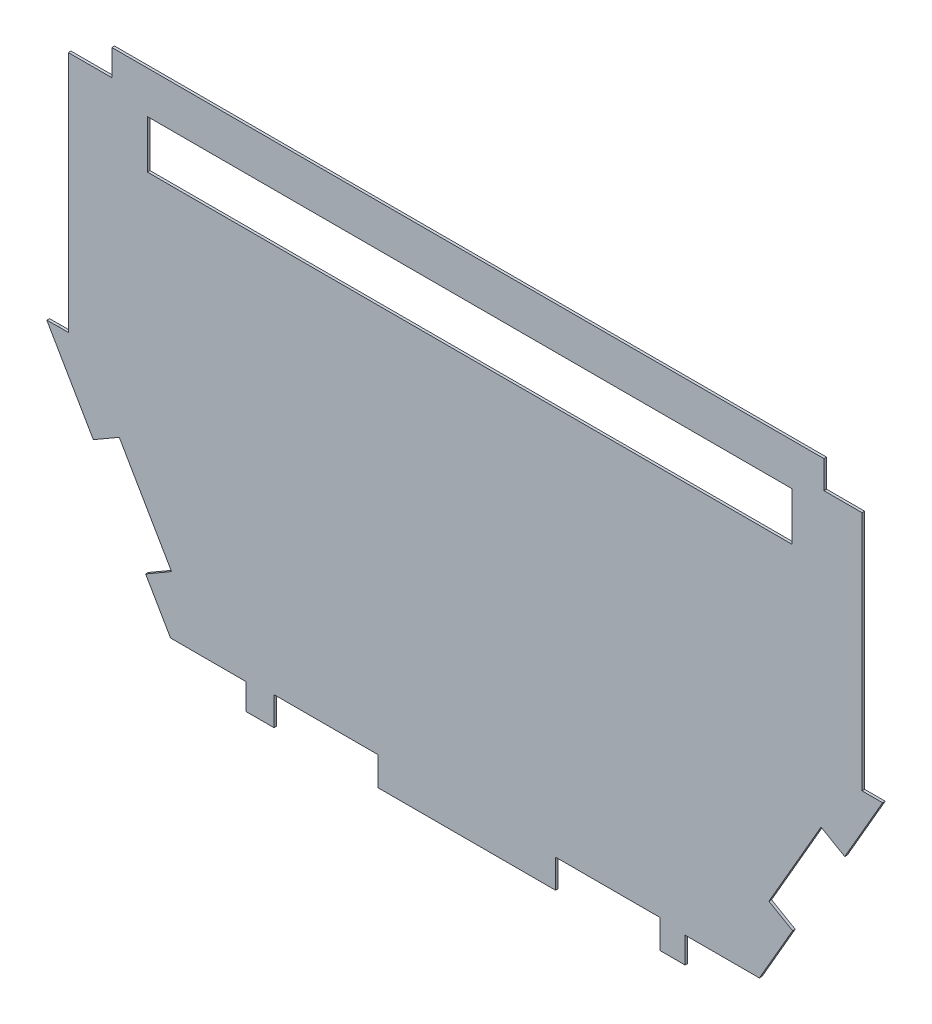
SolidWorks part; units mm, degrees
ref_plane "Front Plane" through (0, 0, 0) normal (0, 0, 1) x (1, 0, 0)
ref_plane "Top Plane" through (0, 0, 0) normal (0, 1, 0) x (1, 0, 0)
ref_plane "Right Plane" through (0, 0, 0) normal (1, 0, 0) x (0, 0, -1)
sketch "Sketch3" plane through (0, 0, 0) normal (0, 0, 1) x (1, 0, 0)
  line L3 (-216.9171, 295.8547) -> (-311.4999, 132.0324)
  line L4 (-368.5466, 112.1234) -> (-705.5135, 112.1234)
  line L7 (-813.3042, 502.1068) -> (-261.9807, 502.1052)
  line L11 (-841.9835, 482.0167) -> (-841.9835, 480.7707)
  line L14 (-232.6774, 480.7707) -> (-233.7869, 480.7707)
  line L16 (-212.2518, 452.135) -> (-212.1921, 346.8689)
  line L18 (-841.9835, 480.7707) -> (-841.9835, 452.932)
  line L21 (-841.9835, 482.0167) -> (-813.3042, 482.0167)
  line L22 (-813.3042, 482.0167) -> (-813.3042, 502.1068)
  line L23 (-862.9682, 452.932) -> (-841.9835, 452.932)
  line L24 (-261.9807, 480.7707) -> (-261.9807, 502.1052)
  line L25 (-233.7869, 480.7707) -> (-261.9807, 480.7707)
  line L26 (-232.6774, 480.7707) -> (-232.6774, 452.135)
  line L27 (-232.6774, 452.135) -> (-212.2518, 452.135)
  line L28 (-862.9682, 452.932) -> (-862.9682, 346.3054)
  line L29 (-212.1921, 346.8689) -> (-232.6774, 346.8689)
  line L30 (-232.6774, 346.8689) -> (-232.6774, 295.8547)
  line L31 (-232.6774, 295.8547) -> (-216.9171, 295.8547)
  line L32 (-368.5466, 112.1234) -> (-368.5466, 132.0324)
  line L33 (-368.5466, 132.0324) -> (-311.4999, 132.0324)
  line L34 (-705.5135, 112.1234) -> (-705.5135, 132.0324)
  line L35 (-705.5135, 132.0324) -> (-763.5115, 132.0324)
  line L36 (-862.9682, 346.3054) -> (-841.9835, 346.3054)
  line L37 (-842.7446, 346.3054) -> (-842.7446, 296.0768)
  line L38 (-842.7446, 296.0768) -> (-858.5136, 295.8547)
  line L39 (-858.5136, 295.8547) -> (-763.5115, 132.0324)
ref_plane "Plane1" through (0, 0, 0) normal (0, 0, 1) x (1, 0, 0)
sketch "Sketch4" plane through (0, 0, 0) normal (0, 0, 1) x (1, 0, 0)
  line L0 (-808.4973, 502.1068) -> (-261.9807, 502.1052)
  line L1 (-261.9807, 502.1052) -> (-261.9807, 480.7707)
  line L2 (-261.9807, 480.7707) -> (-232.6774, 480.7707)
  line L3 (-232.6774, 480.7707) -> (-232.6774, 452.135)
  line L4 (-232.6774, 452.135) -> (-212.2518, 452.135)
  line L5 (-212.2518, 452.135) -> (-212.1921, 346.8689)
  line L6 (-212.1921, 346.8689) -> (-232.6774, 346.8689)
  line L7 (-232.6774, 346.8689) -> (-232.6774, 295.8547)
  line L8 (-232.6774, 295.8547) -> (-216.9171, 295.8547)
  line L9 (-216.9171, 295.8547) -> (-311.4999, 132.0324)
  line L10 (-311.4999, 132.0324) -> (-368.5466, 132.0324)
  line L11 (-368.5466, 132.0324) -> (-368.5466, 112.1234)
  line L12 (-368.5466, 112.1234) -> (-705.5135, 112.1234)
  line L13 (-705.5135, 112.1234) -> (-705.5135, 132.0324)
  line L14 (-705.5135, 132.0324) -> (-763.5115, 132.0324)
  line L15 (-763.5115, 132.0324) -> (-858.5136, 295.8547)
  line L16 (-858.5136, 295.8547) -> (-842.7446, 296.0768)
  line L17 (-842.7446, 296.0768) -> (-842.7446, 346.3054)
  line L18 (-842.7446, 346.3054) -> (-862.9682, 346.3054)
  line L19 (-862.9682, 346.3054) -> (-862.9682, 452.932)
  line L20 (-862.9682, 452.932) -> (-841.9835, 452.932)
  line L21 (-841.9835, 452.932) -> (-841.9835, 482.0167)
  line L22 (-841.9835, 482.0167) -> (-813.3042, 482.0167)
  line L24 (-808.4973, 502.1068) -> (-808.4973, 482.0167)
  line L25 (-813.3042, 482.0167) -> (-808.4973, 482.0167)
extrude "Boss-Extrude1" add sketch "Sketch4" along normal blind 2
sketch "Sketch6" plane through (0, 0, 2) normal (0, 0, 1) x (1, 0, 0)
  line L0 (-822.7867, 234.2471) -> (-802.8902, 245.7853)
  line L1 (-858.5136, 295.8547) -> (-763.5115, 132.0324) construction
  line L2 (-802.8902, 245.7853) -> (-762.7575, 176.58)
  line L3 (-762.7575, 176.58) -> (-782.654, 165.0419)
  line L4 (-782.654, 165.0419) -> (-822.7867, 234.2471)
  dimension "D1" = 80
  dimension "D2" = 23
extrude "Cut-Extrude1" cut sketch "Sketch6" against normal blind 103
sketch "Sketch7" plane through (0, 0, 0) normal (0, 0, -1) x (-1, 0, 0)
  line L0 (245.9886, 245.5014) -> (264.1751, 256.0014)
  line L1 (311.4999, 132.0324) -> (216.9171, 295.8547) construction
  line L2 (264.1751, 256.0014) -> (304.1751, 186.7193)
  line L3 (304.1751, 186.7193) -> (285.9886, 176.2193)
  line L4 (245.9886, 245.5014) -> (285.9886, 176.2193)
  dimension "D1" = 21
  dimension "D2" = 80
extrude "Cut-Extrude2" cut sketch "Sketch7" against normal blind 103
sketch "Sketch8" plane through (0, 0, 2) normal (0, 0, 1) x (1, 0, 0)
  line L1 (-286.3985, 469.8187) -> (-781.3377, 469.8187)
  line L2 (-286.3985, 469.8187) -> (-286.3985, 432.9045)
  line L3 (-286.3985, 432.9045) -> (-781.3377, 432.9045)
  line L4 (-781.3377, 469.8187) -> (-781.3377, 432.9045)
extrude "Cut-Extrude3" cut sketch "Sketch8" against normal blind 103
sketch "Sketch9" plane through (0, 0, 0) normal (0, 0, -1) x (-1, 0, 0)
  line L0 (705.5135, 112.1234) -> (368.5466, 112.1234) construction
  line L1 (387.942, 112.1234) -> (467.942, 112.1234)
  line L2 (387.942, 112.1234) -> (387.942, 134.1234)
  line L3 (387.942, 134.1234) -> (467.942, 134.1234)
  line L4 (467.942, 112.1234) -> (467.942, 134.1234)
  dimension "D1" = 22
  dimension "D2" = 80
extrude "Cut-Extrude4" cut sketch "Sketch9" against normal blind 103
sketch "Sketch10" plane through (0, 0, 0) normal (0, 0, -1) x (-1, 0, 0)
  line L0 (705.5135, 112.1234) -> (467.942, 112.1234) construction
  line L2 (684.1027, 112.1234) -> (604.1027, 112.1234)
  line L3 (684.1027, 112.1234) -> (684.1027, 134.1234)
  line L4 (684.1027, 134.1234) -> (604.1027, 134.1234)
  line L5 (604.1027, 112.1234) -> (604.1027, 134.1234)
  point P0 (684.1027, 112.1234)
  dimension "D3" = 80
  dimension "D4" = 22
extrude "Cut-Extrude5" cut sketch "Sketch10" against normal blind 10
sketch "Sketch18" plane through (0, 0, 0) normal (0, 0, -1) x (-1, 0, 0)
  line L0 (232.6774, 337.8603) -> (232.6774, 496.2238)
  line L1 (232.6774, 295.8547) -> (232.6774, 346.8689) construction
  line L2 (232.6774, 496.2238) -> (155.7129, 496.2238)
  line L3 (155.7129, 496.2238) -> (155.7129, 334.1516)
  line L4 (155.7129, 334.1516) -> (232.6774, 334.1516)
  line L5 (232.6774, 334.1516) -> (232.6774, 337.8603)
extrude "Cut-Extrude26" cut sketch "Sketch18" against normal blind 50
sketch "Sketch20" plane through (0, 0, 0) normal (0, 0, -1) x (-1, 0, 0)
  line L1 (841.9835, 482.0167) -> (965.492, 482.0167)
  line L2 (841.9835, 482.0167) -> (841.9835, 295.9782)
  line L3 (841.9835, 295.9782) -> (965.492, 295.9782)
  line L4 (965.492, 482.0167) -> (965.492, 295.9782)
extrude "Cut-Extrude27" cut sketch "Sketch20" against normal blind 50
